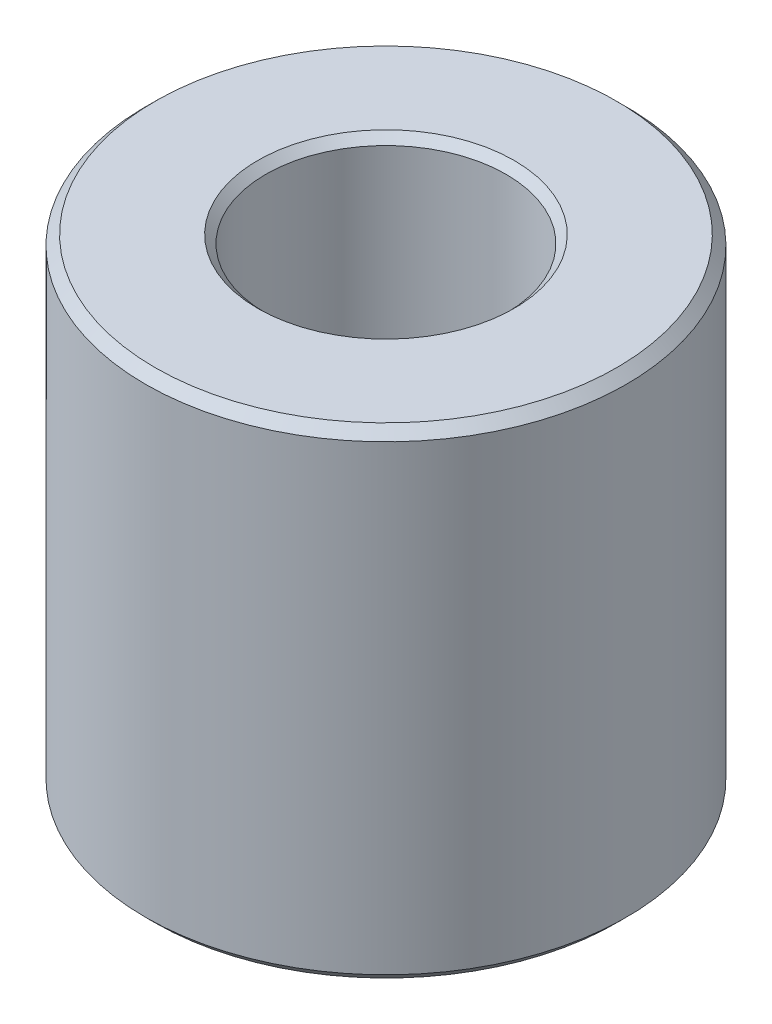
SolidWorks part; units mm, degrees
material "C71500"
ref_plane "Front" through (0, 0, 0) normal (0, 0, 1) x (1, 0, 0)
ref_plane "Top" through (0, 0, 0) normal (0, 1, 0) x (1, 0, 0)
ref_plane "Right" through (0, 0, 0) normal (1, 0, 0) x (0, 0, -1)
sketch "Sketch1" plane through (0, 0, 0) normal (0, 1, 0) x (1, 0, 0)
  circle A0 centre (0, 0) radius 19.05
  dimension "D1" = 38.1
extrude "Extrude1" add sketch "Sketch1" along normal blind 38.1
hole_wizard "3/4 (0.75) Diameter Hole1" positions "Sketch3" profile "Sketch2" hole size "3/4" standard "Ansi Inch" end condition through all
sketch "Sketch3" plane through (0, 38.1, 0) normal (0, 1, 0) x (-1, 0, 0)
  point P0 (0, 0)
sketch "Sketch2" plane through (0, 38.1, 0) normal (1, 0, 0) x (0, 0, 1)
  line L0 (0, 0) -> (0, 38.1)
  line L1 (0, 38.1) -> (10.16, 38.1)
  line L2 (9.525, 37.465) -> (9.525, 0.635)
  line L3 (9.525, 0.635) -> (10.16, 0)
  line L5 (10.16, 0) -> (0, 0)
  line L6 (-9.525, 0.635) -> (-10.16, 0) construction
  line L7 (10.16, 38.1) -> (9.525, 37.465)
  line L8 (-10.16, 38.1) -> (-9.525, 37.465) construction
  line L11 (0, -6.35) -> (0, 107.95) construction
  dimension "Thru Hole Dia." = 19.05
  dimension "Thru Hole Depth" = 38.1
  dimension "Near C'Sink Dia." = 20.32
  dimension "Near C'Sink Angle" = 90
  dimension "Far C'Sink Dia." = 20.32
  dimension "Far C'Sink Angle" = 90
chamfer "Chamfer1" distance 0.762 angle 45 2 edges at (0, 0, 19.05) (0, 38.1, 19.05)
